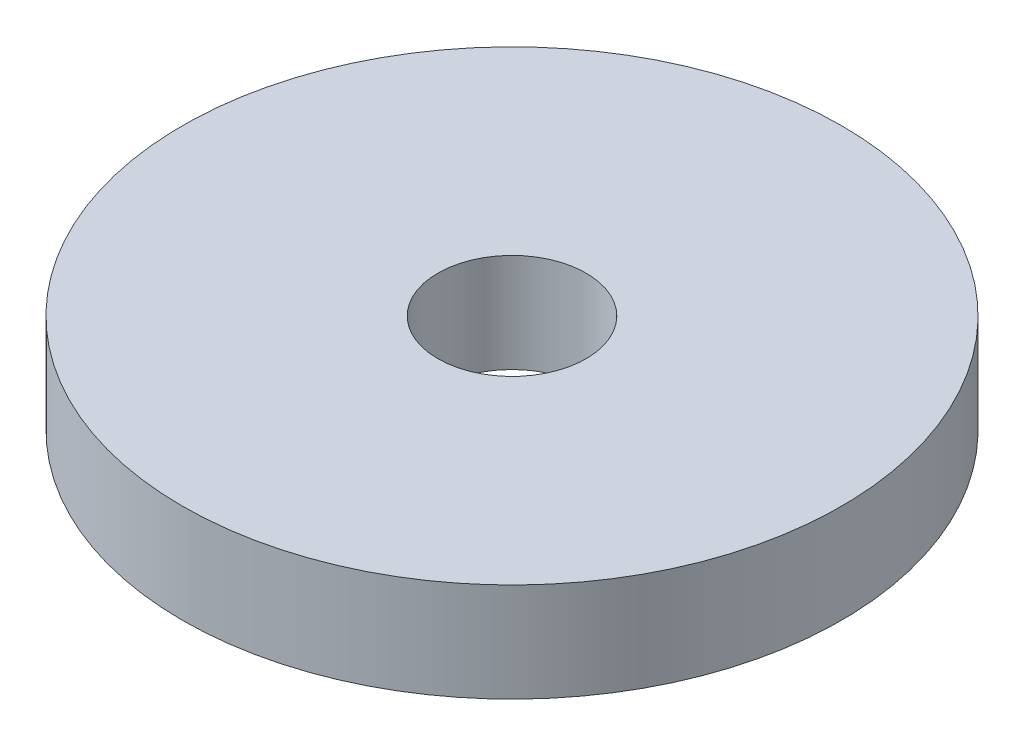
SolidWorks part; units mm, degrees
ref_plane "Front" through (0, 0, 0) normal (0, 0, 1) x (1, 0, 0)
ref_plane "Top" through (0, 0, 0) normal (0, 1, 0) x (1, 0, 0)
ref_plane "Right" through (0, 0, 0) normal (1, 0, 0) x (0, 0, -1)
sketch "Sketch1" plane through (0, 0, 0) normal (0, 1, 0) x (1, 0, 0)
  circle A0 centre (0, 0) radius 10
  circle A1 centre (0, 0) radius 2.25
  dimension "D1" = 20
  dimension "D2" = 4.5
extrude "Boss-Extrude1" add sketch "Sketch1" along normal blind 3
